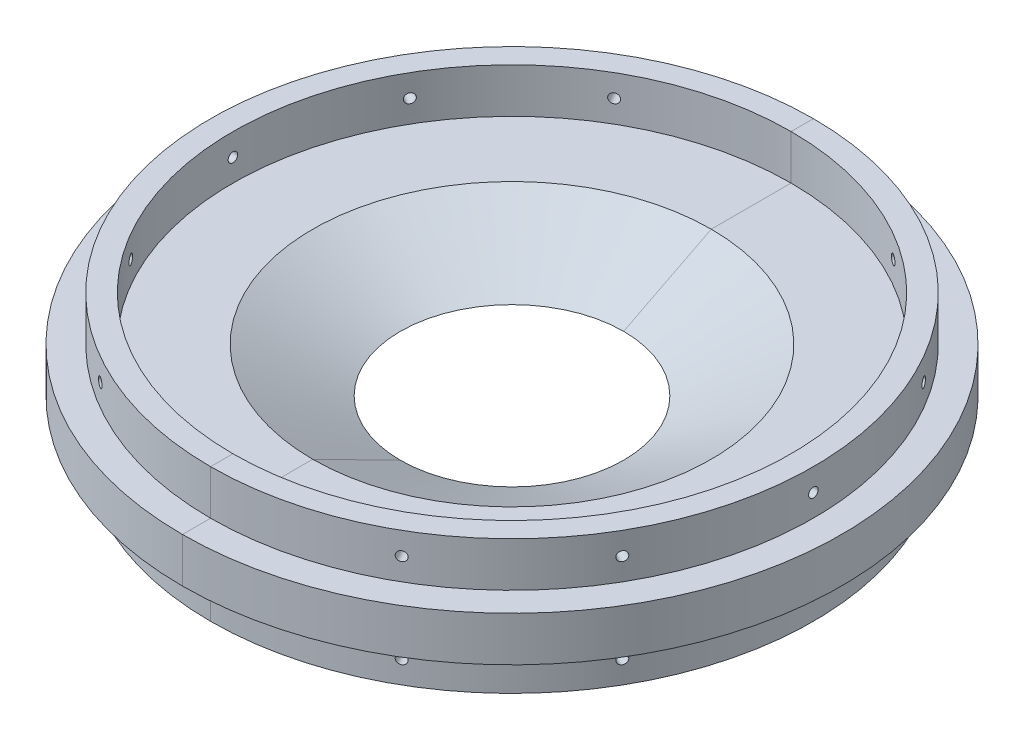
SolidWorks part; units mm, degrees
ref_plane "Front Plane" through (0, 0, 0) normal (0, 0, 1) x (1, 0, 0)
ref_plane "Top Plane" through (0, 0, 0) normal (0, 1, 0) x (1, 0, 0)
ref_plane "Right Plane" through (0, 0, 0) normal (1, 0, 0) x (0, 0, -1)
sketch "Sketch1" plane through (0, 0, 0) normal (0, 1, 0) x (1, 0, 0)
  circle A0 centre (0, 0) radius 93.726
  circle A1 centre (0, 0) radius 31.75
  dimension "D1" = 187.452
  dimension "D2" = 63.5
extrude "Boss-Extrude1" add sketch "Sketch1" along normal mid plane 12.7
sketch "Sketch5" plane through (0, 6.35, 0) normal (0, 1, 0) x (1, 0, 0)
  circle A0 centre (0, 0) radius 85.725
  circle A1 centre (0, 0) radius 79.375
  dimension "D1" = 171.45
  dimension "D2" = 158.75
extrude "Boss-Extrude2" add sketch "Sketch5" along normal blind 12.7
ref_plane "Plane1" through (0, 0, -85.725) normal (0, 0, -1) x (-1, 0, 0)
sketch "Sketch6" plane through (0, 0, -85.725) normal (0, 0, -1) x (-1, 0, 0)
  line L0 (0, 13.97) -> (0, -13.97) construction
  line L1 (93.726, 6.35) -> (-93.726, 6.35) construction
  circle A0 centre (0, 12.7) radius 1.3525
  dimension "D1" = 2.7051
  dimension "D2" = 6.35
extrude "Cut-Extrude1" cut sketch "Sketch6" against normal blind 12.7
pattern_circular "CirPattern1" count 12 over 360 about axis through (0, 6.35, 0) along (0, -1, 0) of "Cut-Extrude1"
mirror "Mirror1" about plane through (0, 0, 0) normal (0, 1, 0) of "CirPattern1", "Cut-Extrude1", "Boss-Extrude2"
sketch "Sketch7" plane through (0, 19.05, 0) normal (0, 1, 0) x (1, 0, 0)
  line L0 (-25.7878, 75.0692) -> (-28.1663, 80.9657)
  line L1 (28.1663, 80.9657) -> (25.7878, 75.0692)
  arc A0 (28.1663, 80.9657) -> (-28.1663, 80.9657) centre (0, 0) ccw
  circle A1 centre (0, 0) radius 85.725 construction
  arc A2 (25.7878, 75.0692) -> (-25.7878, 75.0692) centre (0, 0) ccw
  circle A3 centre (0, 0) radius 79.375 construction
extrude "Boss-Extrude3" add sketch "Sketch7" against normal up to surface (25.4 mm away)
mirror "Mirror3" about plane through (0, 0, 0) normal (0, 1, 0) of "Boss-Extrude3"
mirror "Mirror4" about plane through (0, 0, 0) normal (0, 0, 1) of "Boss-Extrude3"
mirror "Mirror5" about plane through (0, 0, 0) normal (0, 1, 0) of "Mirror4"
sketch "Sketch4" plane through (0, 0, 0) normal (0, 0, 1) x (1, 0, 0)
  line L0 (0, 23.2786) -> (0, -14.9525) construction
sketch "Sketch3" plane through (0, 0, 0) normal (0, 0, 1) x (1, 0, 0)
  line L0 (-31.75, -6.35) -> (-56.6752, 6.35)
  line L1 (93.726, 6.35) -> (-93.726, 6.35) construction
  line L2 (-56.6752, 6.35) -> (-31.75, 6.35)
  line L3 (-31.75, 6.35) -> (-31.75, -6.35)
  line L4 (-31.75, -6.35) -> (31.75, -6.35) construction
  line L5 (31.75, 6.35) -> (-31.75, 6.35) construction
  dimension "D1" = 27
revolve "Cut-Revolve1" cut sketch "Sketch3" angle 360 about L0
split "Split1" trim tools "Right Plane" bodies to split 103 resulting bodies 104 105
